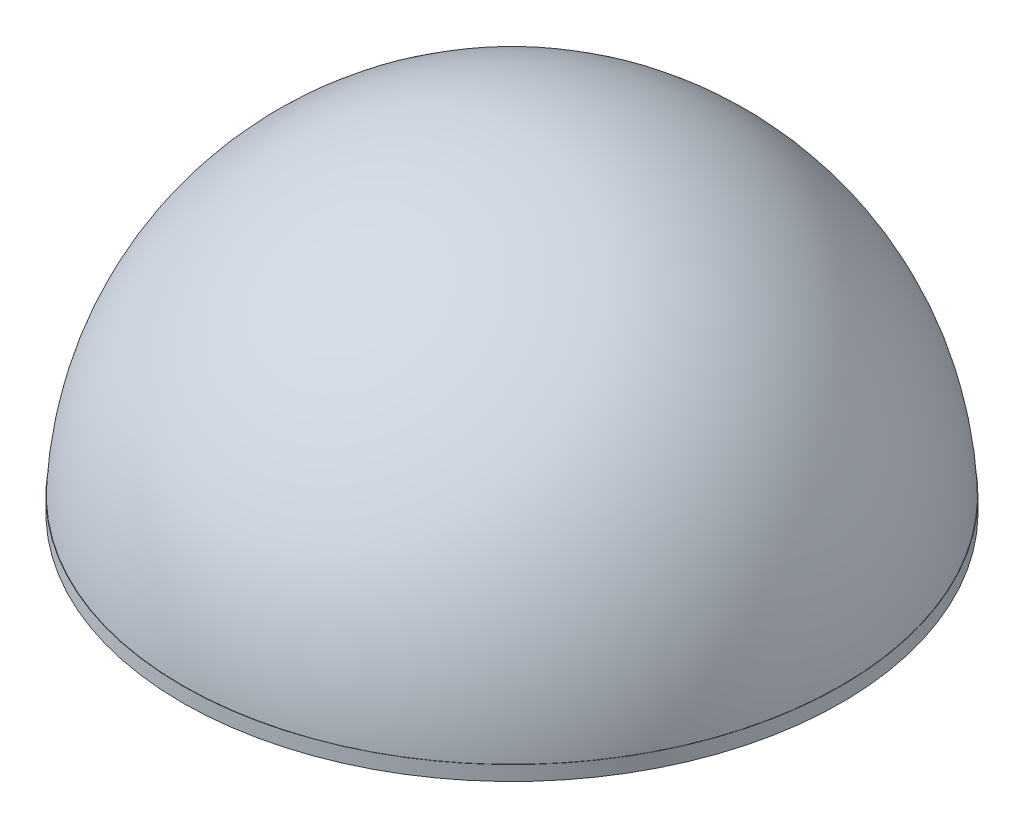
SolidWorks part; units mm, degrees
material "Glass"
ref_plane "Front Plane" through (0, 0, 0) normal (0, 0, 1) x (1, 0, 0)
ref_plane "Top Plane" through (0, 0, 0) normal (0, 1, 0) x (1, 0, 0)
ref_plane "Right Plane" through (0, 0, 0) normal (1, 0, 0) x (0, 0, -1)
sketch "Sketch1" plane through (0, 0, 0) normal (0, 0, 1) x (1, 0, 0)
  line L0 (0, 45) -> (0, 0)
  line L2 (0, 0) -> (45, 0)
  arc A0 (45, 0) -> (0, 45) centre (0, 0) ccw
revolve "Revolve1" add sketch "Sketch1" angle 360 about L0
shell "Shell1" thickness 2
sketch "Sketch2" plane through (0, 0, 0) normal (0, 1, 0) x (1, 0, 0)
  circle A0 centre (0, 0) radius 45
sketch "Sketch3" plane through (0, 0, 0) normal (0, 0, 1) x (1, 0, 0)
  line L0 (0, 30) -> (0, 0)
  line L1 (-10, 0) -> (0, 0)
  line L2 (-10, 30) -> (-10, 0)
  line L3 (-10, 30) -> (0, 30)
  line L4 (0, 54.433) -> (0, -14.1322) construction
  line L5 (-10, 54.433) -> (-10, -14.1322) construction
  line L6 (-58.2057, 30) -> (51.9045, 30) construction
  line L7 (-58.2057, 0) -> (51.9045, 0) construction
  dimension "D1" = 10
  dimension "D2" = 30
revolve "Revolve2" add sketch "Sketch3" angle 360 about L0
fillet "Fillet1" radius 1 1 edges at (0, 30, 10)
extrude "Boss-Extrude2" add sketch "Sketch2" along normal blind 2
